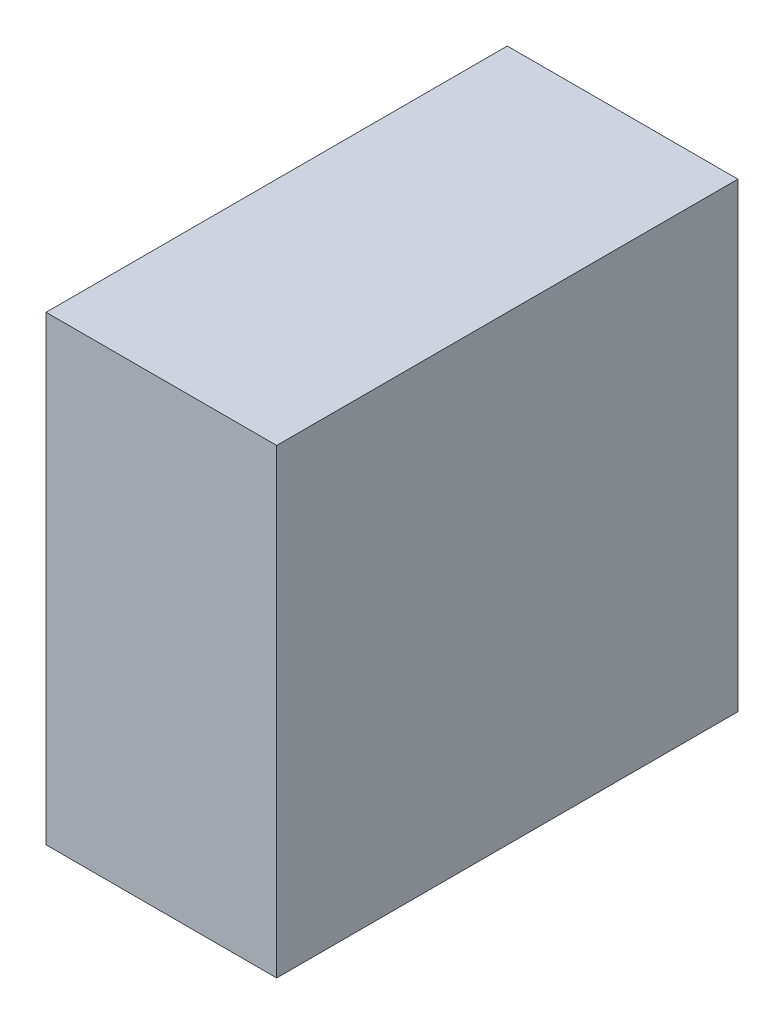
SolidWorks part; units mm, degrees
ref_plane "Front Plane" through (0, 0, 0) normal (0, 0, 1) x (1, 0, 0)
ref_plane "Top Plane" through (0, 0, 0) normal (0, 1, 0) x (1, 0, 0)
ref_plane "Right Plane" through (0, 0, 0) normal (1, 0, 0) x (0, 0, -1)
sketch "Sketch1" plane through (0, 0, 0) normal (0, 0, 1) x (1, 0, 0)
  line L1 (0, 0) -> (40, 0)
  line L2 (0, 0) -> (0, 40)
  line L3 (0, 40) -> (40, 40)
  line L4 (40, 0) -> (40, 40)
  dimension "D1" = 40
  dimension "D2" = 40
extrude "Boss-Extrude1" add sketch "Sketch1" along normal blind 40
sketch "Sketch2" plane through (0, 0, 40) normal (0, 0, 1) x (1, 0, 0)
  line L0 (0, 0) -> (20, 40)
  line L1 (40, 40) -> (0, 40) construction
  line L2 (20, 40) -> (0, 40)
  line L3 (0, 40) -> (0, 0)
extrude "Cut-Extrude1" cut sketch "Sketch2" against normal blind 40
sketch "Sketch3" plane through (0, 0, 40) normal (0, 0, 1) x (1, 0, 0)
  line L0 (20, 40) -> (20, 0)
  line L1 (0, 0) -> (40, 0) construction
  line L2 (20, 0) -> (0, 0)
  line L3 (0, 0) -> (20, 40)
extrude "Cut-Extrude2" cut sketch "Sketch3" against normal blind 20
